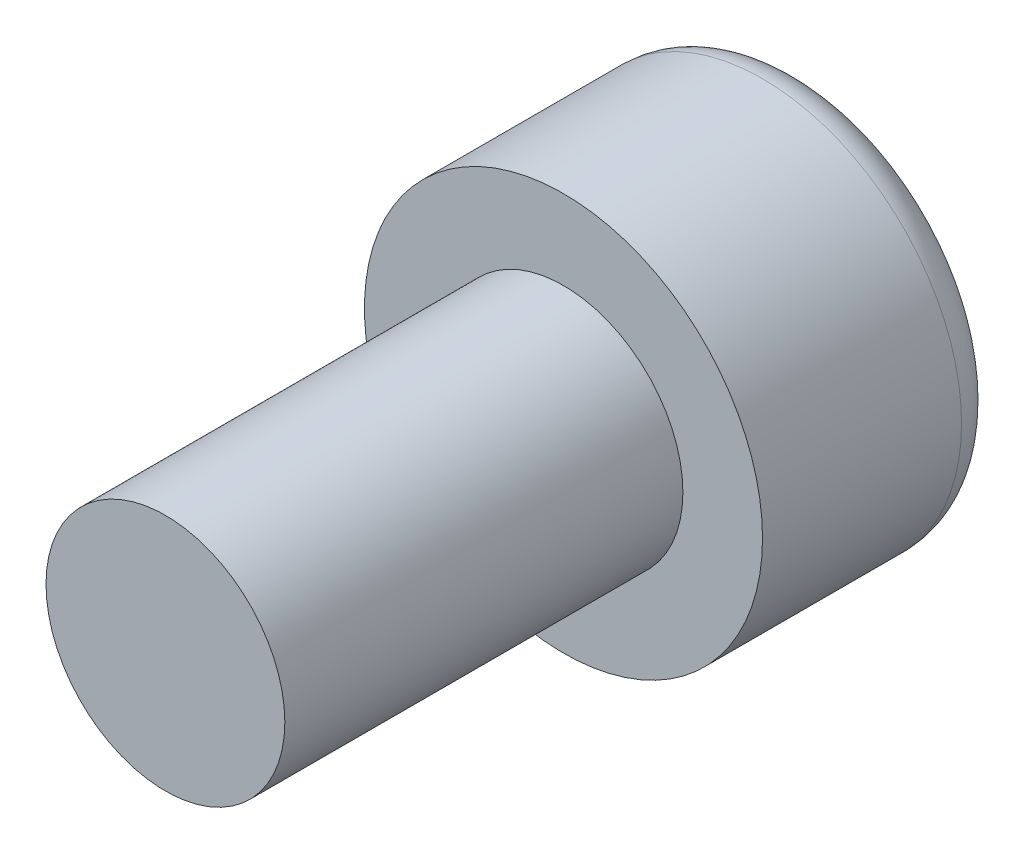
SolidWorks part; units mm, degrees
ref_plane "正面" through (0, 0, 0) normal (0, 0, 1) x (1, 0, 0)
ref_plane "平面" through (0, 0, 0) normal (0, 1, 0) x (1, 0, 0)
ref_plane "右側面" through (0, 0, 0) normal (1, 0, 0) x (0, 0, -1)
sketch "ｽｹｯﾁ1" plane through (0, 0, 0) normal (0, 0, 1) x (1, 0, 0)
  circle A0 centre (0, 0) radius 5
  dimension "D1" = 10
extrude "ﾎﾞｽ - 押し出し1" add sketch "ｽｹｯﾁ1" along normal blind 6
sketch "ｽｹｯﾁ2" plane through (0, 0, 6) normal (0, 0, 1) x (1, 0, 0)
  circle A0 centre (0, 0) radius 3
  dimension "D1" = 6
extrude "ﾎﾞｽ - 押し出し2" add sketch "ｽｹｯﾁ2" along normal blind 10
sketch "ｽｹｯﾁ3" plane through (0, 0, 0) normal (0, 0, -1) x (-1, 0, 0)
  line L1 (-2.5, -1.4434) -> (0, -2.8868)
  line L2 (0, -2.8868) -> (2.5, -1.4434)
  line L3 (2.5, -1.4434) -> (2.5, 1.4434)
  line L4 (2.5, 1.4434) -> (0, 2.8868)
  line L5 (0, 2.8868) -> (-2.5, 1.4434)
  line L6 (-2.5, 1.4434) -> (-2.5, -1.4434)
  circle A0 centre (0, 0) radius 2.5 construction
  dimension "D1" = 5
extrude "ｶｯﾄ - 押し出し1" cut sketch "ｽｹｯﾁ3" against normal blind 3
fillet "ﾌｨﾚｯﾄ1" radius 1 1 edges at (5, 0, 0)
